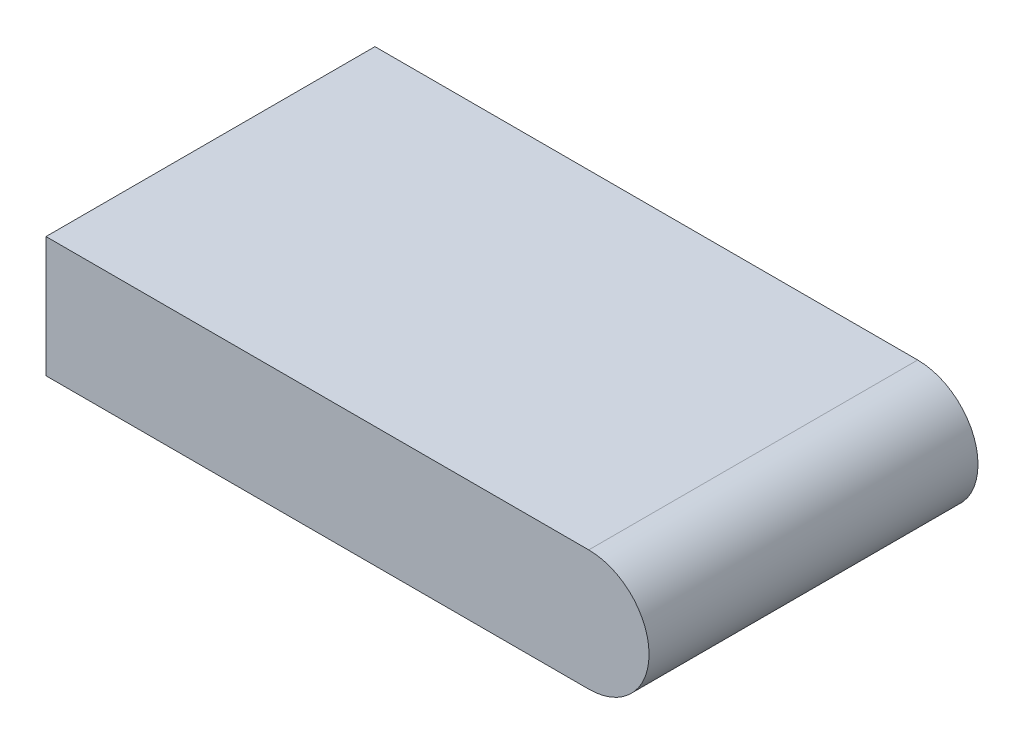
SolidWorks part; units mm, degrees
ref_plane "Front Plane" through (0, 0, 0) normal (0, 0, 1) x (1, 0, 0)
ref_plane "Top Plane" through (0, 0, 0) normal (0, 1, 0) x (1, 0, 0)
ref_plane "Right Plane" through (0, 0, 0) normal (1, 0, 0) x (0, 0, -1)
sketch "Sketch2" plane through (0, 0, 0) normal (0, 1, 0) x (1, 0, 0)
  line L1 (0, 0) -> (49.5, 0)
  line L2 (0, 0) -> (0, 30)
  line L3 (0, 30) -> (49.5, 30)
  line L4 (49.5, 0) -> (49.5, 30)
  dimension "D1" = 30
  dimension "D2" = 49.5
extrude "Boss-Extrude1" add sketch "Sketch2" along normal blind 11
sketch "Sketch4" plane through (0, 0, -30) normal (0, 0, -1) x (-1, 0, 0)
  line L0 (-49.5, 11) -> (-49.5, 0) construction
  circle A0 centre (-49.5, 5.5) radius 5.5
  point P5 (-49.5, 5.5)
extrude "Boss-Extrude2" add sketch "Sketch4" against normal blind 30
